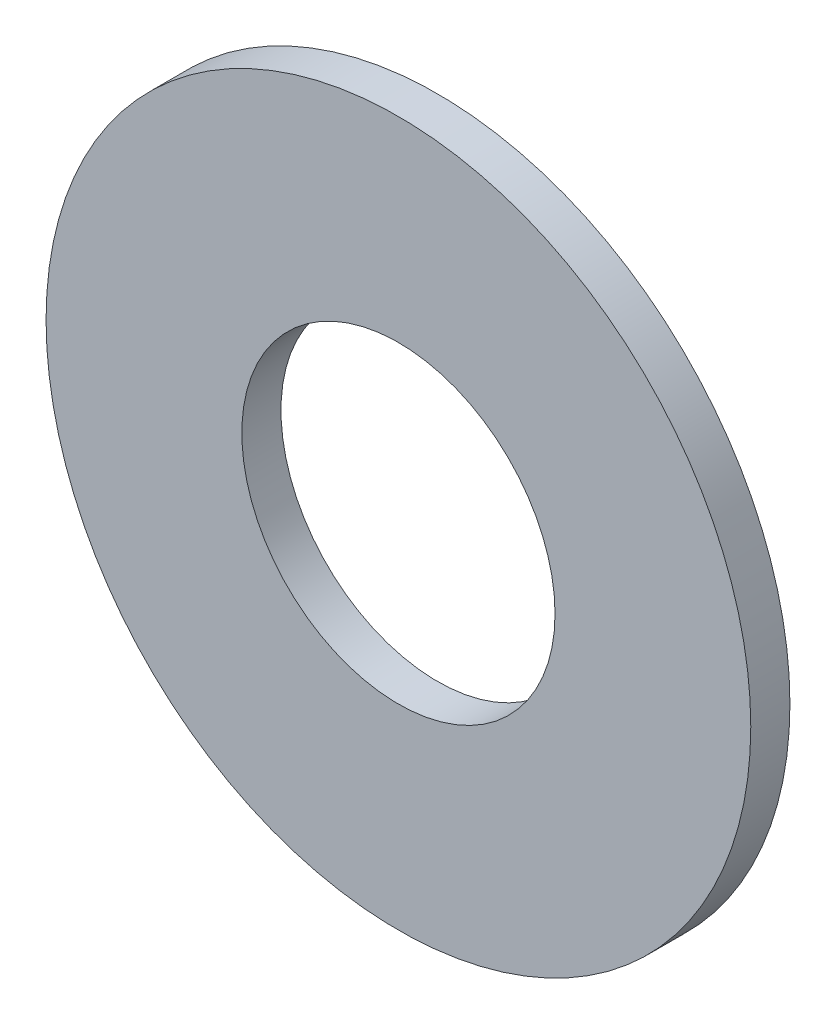
SolidWorks part; units mm, degrees
material "1.5714 (16NiCr4)"
ref_plane "Alzado" through (0, 0, 0) normal (0, 0, 1) x (1, 0, 0)
ref_plane "Planta" through (0, 0, 0) normal (0, 1, 0) x (1, 0, 0)
ref_plane "Vista lateral" through (0, 0, 0) normal (1, 0, 0) x (0, 0, -1)
sketch "Croquis1" plane through (0, 0, 0) normal (0, 0, 1) x (1, 0, 0)
  circle A0 centre (0, 0) radius 4
  circle A1 centre (0, 0) radius 9
  dimension "D1" = 8
  dimension "D2" = 18
extrude "Saliente-Extruir1" add sketch "Croquis1" along normal blind 1
